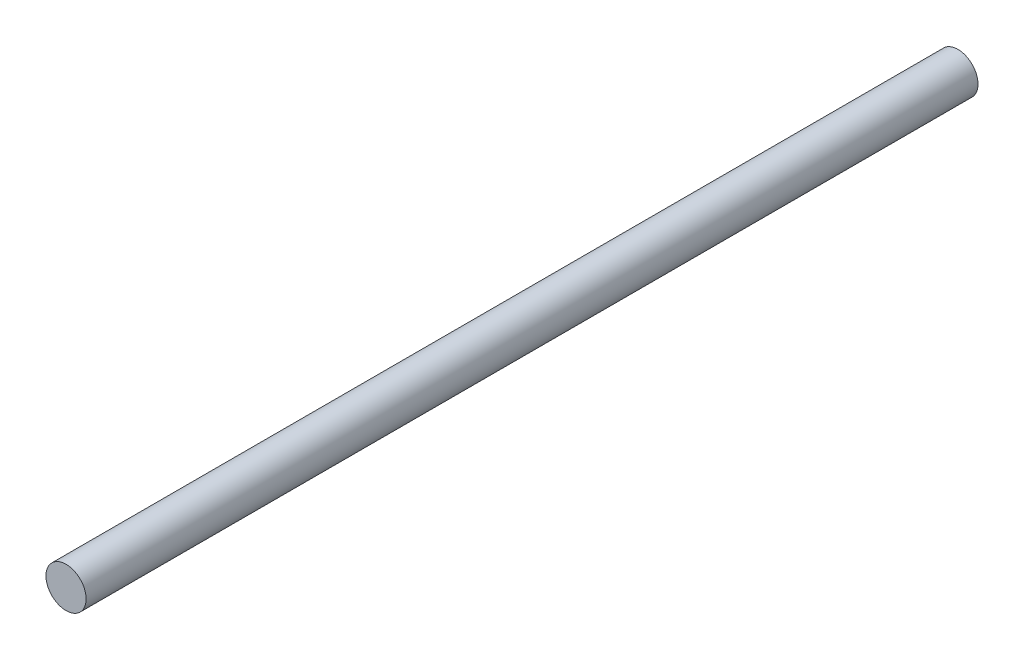
SolidWorks part; units mm, degrees
material "6061 Alloy"
ref_plane "Front Plane" through (0, 0, 0) normal (0, 0, 1) x (1, 0, 0)
ref_plane "Top Plane" through (0, 0, 0) normal (0, 1, 0) x (1, 0, 0)
ref_plane "Right Plane" through (0, 0, 0) normal (1, 0, 0) x (0, 0, -1)
sketch "Sketch1" plane through (0, 0, 0) normal (0, 0, 1) x (1, 0, 0)
  circle A0 centre (0, 0) radius 2.5
  dimension "D1" = 5
extrude "Boss-Extrude1" add sketch "Sketch1" along normal blind 111
